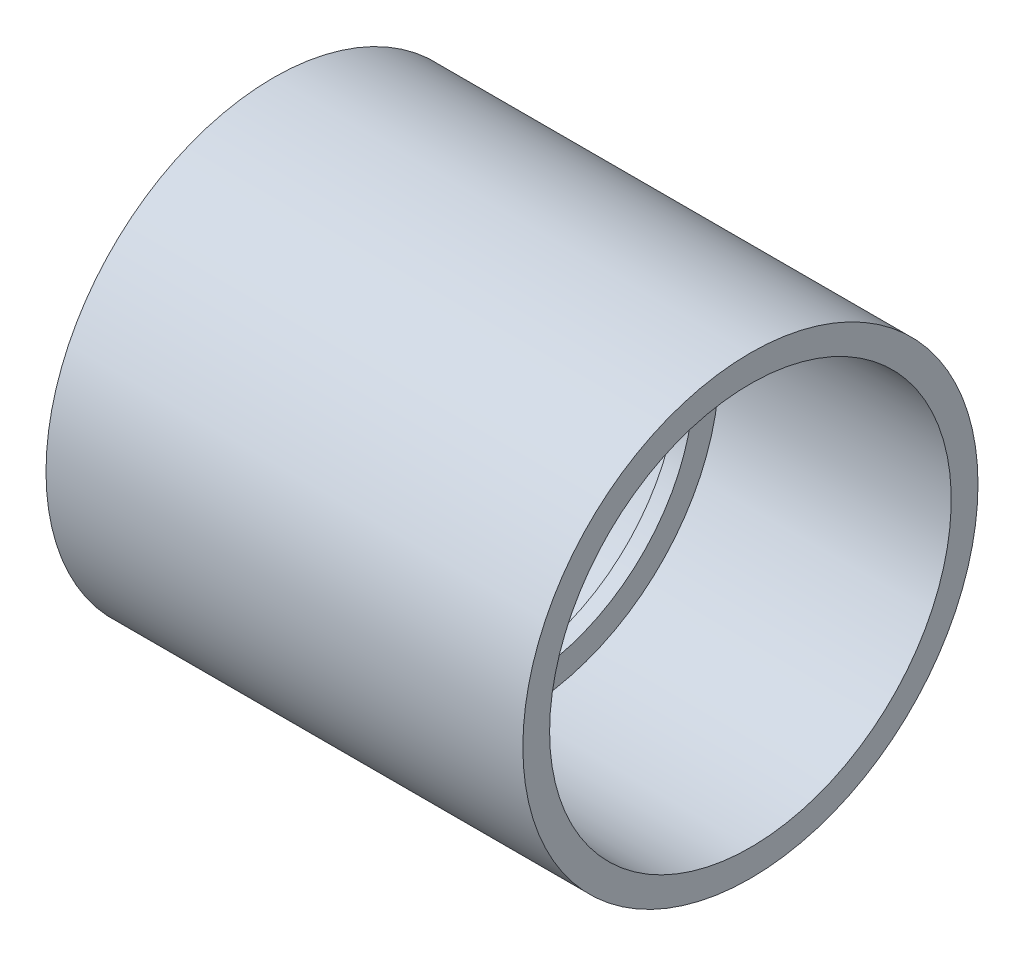
SolidWorks part; units mm, degrees
ref_plane "Front Plane" through (0, 0, 0) normal (0, 0, 1) x (1, 0, 0)
ref_plane "Top Plane" through (0, 0, 0) normal (0, 1, 0) x (1, 0, 0)
ref_plane "Right Plane" through (0, 0, 0) normal (1, 0, 0) x (0, 0, -1)
sketch "Sketch0" plane through (0, 0, 0) normal (0, 0, 1) x (1, 0, 0)
  line L0 (-35.9918, 0) -> (1.1938, 0) construction
  line L2 (-1.1938, 0) -> (1.1938, 0) construction
  line L3 (-35.9918, 0) -> (35.9918, 0) construction
  line L4 (-35.9918, 34.3535) -> (-35.9918, -34.3535) construction
  line L5 (-1.1938, 30.0863) -> (-35.9918, 30.3149) construction
  line L6 (-1.1938, 30.0863) -> (-1.1938, -30.0863) construction
  line L7 (-1.1938, -30.0863) -> (-35.9918, -30.3149) construction
  line L8 (-35.9918, 30.3149) -> (-35.9918, -30.3149) construction
  line L14 (-1.1938, 26.2509) -> (-1.1938, -26.2509) construction
  dimension "N" = 2.3876
  dimension "M" = 68.707
  dimension "OD A" = 60.6298
  dimension "OD B" = 60.1726
  dimension "ID" = 52.5018
  dimension "L" = 71.9836
sketch "Sketch1" plane through (0, 0, 0) normal (0, 0, 1) x (1, 0, 0)
  line L0 (-35.9918, 0) -> (1.1938, 0) construction
  line L1 (-35.9918, 0) -> (1.1938, 0) construction
  line L2 (-1.1938, -26.2509) -> (1.1938, -26.2509)
  line L3 (35.9918, -30.3149) -> (1.1938, -30.0863)
  line L4 (-35.9918, -34.3535) -> (-35.9918, -30.3149)
  line L5 (-35.9918, -30.3149) -> (-1.1938, -30.0863)
  line L6 (35.9918, -34.3535) -> (35.9918, -30.3149)
  line L7 (-1.1938, -30.0863) -> (-1.1938, -26.2509)
  line L8 (1.1938, -30.0863) -> (1.1938, -26.2509)
  line L9 (35.9918, -34.3535) -> (-35.9918, -34.3535)
  line L10 (0, 0) -> (0, -26.2509) construction
revolve "Revolve1" add sketch "Sketch1" angle 360 about L1
